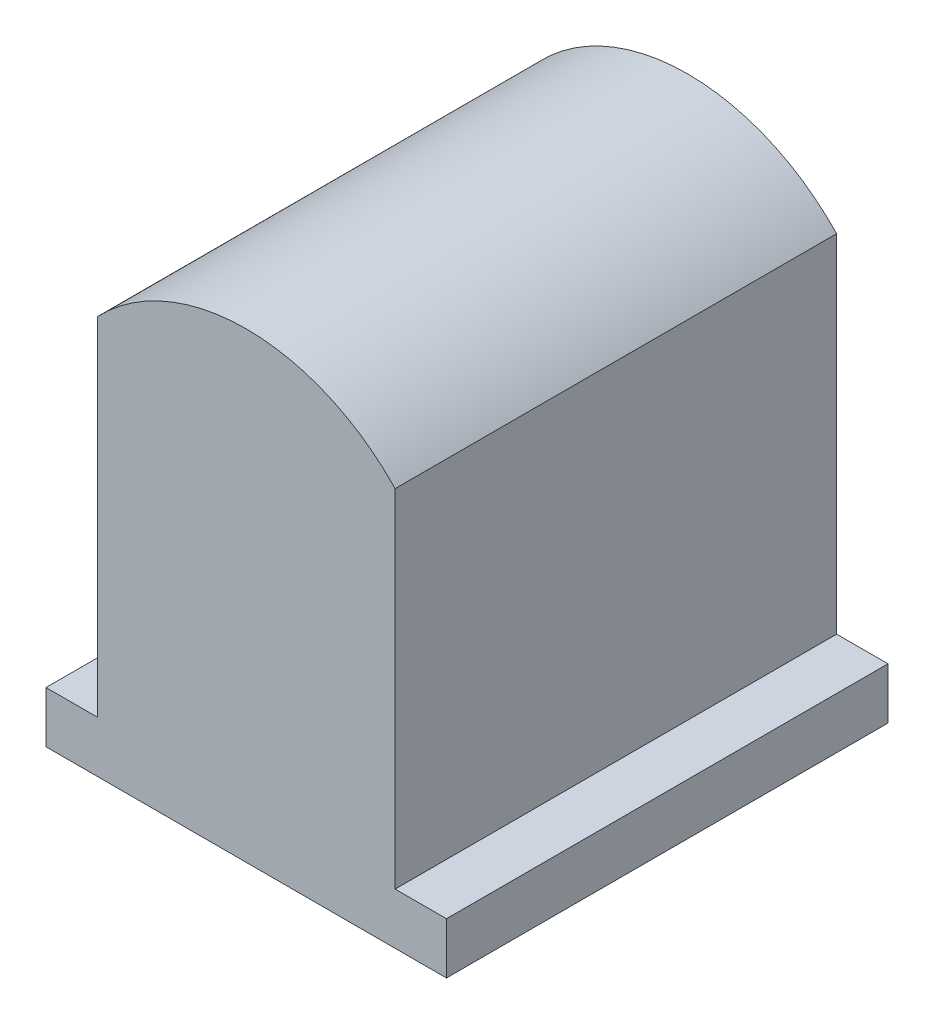
SolidWorks part; units mm, degrees
material "PA Typ 6"
ref_plane "Płaszczyzna przednia" through (0, 0, 0) normal (0, 0, 1) x (1, 0, 0)
ref_plane "Płaszczyzna górna" through (0, 0, 0) normal (0, 1, 0) x (1, 0, 0)
ref_plane "Płaszczyzna prawa" through (0, 0, 0) normal (1, 0, 0) x (0, 0, -1)
sketch "Szkic1" plane through (0, 0, 0) normal (0, 0, 1) x (1, 0, 0)
  line L0 (-1.45, -1.4387) -> (-1.95, -1.4387)
  line L1 (-1.45, -1.9387) -> (1.45, -1.9387)
  line L2 (-1.45, -1.4387) -> (-1.45, 1.9387)
  line L4 (1.45, -1.4387) -> (1.45, 1.9387)
  line L5 (-1.45, -1.9387) -> (1.45, 1.9387) construction
  line L6 (-1.45, 1.9387) -> (1.45, -1.9387) construction
  line L7 (-1.95, -1.4387) -> (-1.95, -1.9387)
  line L8 (-1.95, -1.9387) -> (-1.45, -1.9387)
  line L9 (1.45, -1.4387) -> (1.95, -1.4387)
  line L10 (1.95, -1.4387) -> (1.95, -1.9387)
  line L11 (1.95, -1.9387) -> (1.45, -1.9387)
  arc A0 (-1.45, 1.9387) -> (1.45, 1.9387) centre (0, 0.5613) cw
  point P0 (0, 0)
  point P7 (0, 2.5613)
  dimension "D2" = 2
  dimension "D1" = 2.9
  dimension "D3" = 4.5
  dimension "D4" = 3.8775
  dimension "D5" = 0.5
  dimension "D6" = 0.5
extrude "Dodanie-wyciągnięcie1" add sketch "Szkic1" along normal blind 4.3
ref_plane "Płaszczyzna1" through (0, 0, 2.15) normal (0, 0, 1) x (1, 0, 0)
